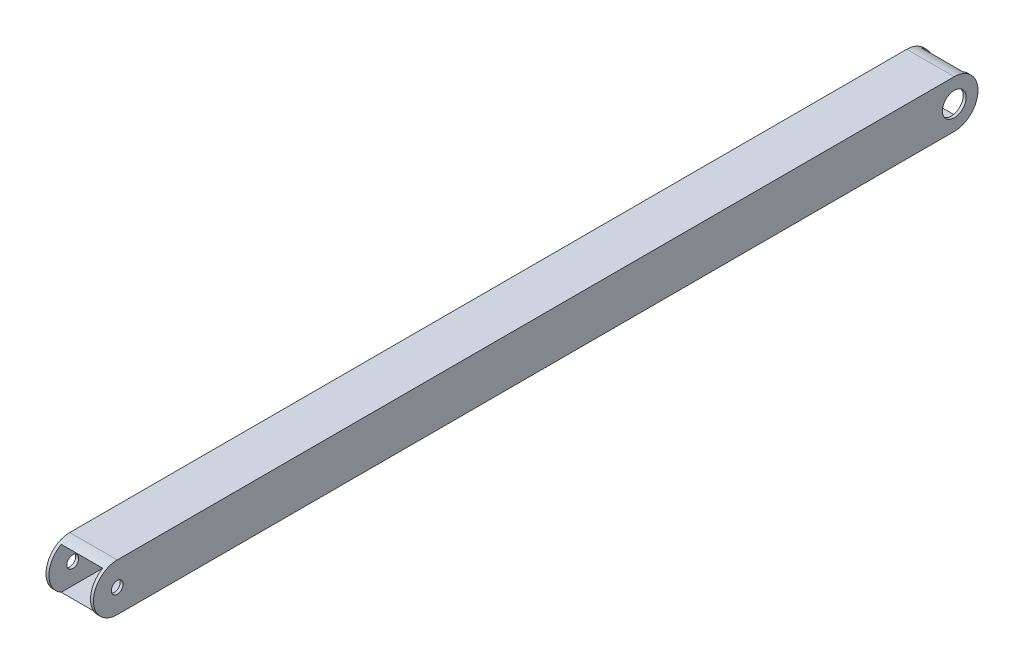
SolidWorks part; units mm, degrees
ref_plane "Front Plane" through (0, 0, 0) normal (0, 0, 1) x (1, 0, 0)
ref_plane "Top Plane" through (0, 0, 0) normal (0, 1, 0) x (1, 0, 0)
ref_plane "Right Plane" through (0, 0, 0) normal (1, 0, 0) x (0, 0, -1)
sketch "Sketch1" plane through (0, 0, 0) normal (0, 0, 1) x (1, 0, 0)
  line L0 (-11.1125, 11.1125) -> (11.1125, 11.1125)
  line L1 (-12.7, 12.7) -> (12.7, 12.7)
  line L2 (-12.7, 12.7) -> (-12.7, -12.7)
  line L3 (-12.7, -12.7) -> (12.7, -12.7)
  line L4 (12.7, 12.7) -> (12.7, -12.7)
  line L5 (-12.7, 12.7) -> (12.7, -12.7) construction
  line L6 (-12.7, -12.7) -> (12.7, 12.7) construction
  line L7 (11.1125, 11.1125) -> (11.1125, -11.1125)
  line L8 (-11.1125, -11.1125) -> (11.1125, -11.1125)
  line L9 (-11.1125, 11.1125) -> (-11.1125, -11.1125)
  point P0 (0, 0)
  dimension "D1" = 25.4
  dimension "D2" = 25.4
  dimension "D3" = 1.5875
extrude "Boss-Extrude1" add sketch "Sketch1" along normal blind 473.2274
sketch "Sketch2" plane through (12.7, 0, 0) normal (1, 0, 0) x (0, 0, -1)
  line L0 (-473.2274, 12.7) -> (-460.5274, 12.7) construction
  line L1 (-473.2274, 12.7) -> (0, 12.7) construction
  line L2 (-460.5274, 12.7) -> (-460.5274, -12.7) construction
  line L3 (-473.2274, -12.7) -> (0, -12.7) construction
  line L4 (-473.2274, 12.7) -> (-460.5274, 12.7)
  line L5 (-473.2274, 12.7) -> (-473.2274, -12.7)
  line L6 (-473.2274, -12.7) -> (-460.5274, -12.7)
  arc A0 (-460.5274, 12.7) -> (-460.5274, -12.7) centre (-460.5274, 0) ccw
  line M3 (0, 12.7) -> (-473.2274, 12.7)
  line M4 (-473.2274, 12.7) -> (-473.2274, -12.7)
  line M5 (-473.2274, -12.7) -> (0, -12.7)
  dimension "D1" = 12.7
extrude "Cut-Extrude1" cut sketch "Sketch2" against normal through all contours A0 M3 M4 | A0 L5 M5
sketch "Sketch3" plane through (12.7, 0, 0) normal (1, 0, 0) x (0, 0, -1)
  line L0 (-460.5274, -12.7) -> (0, -12.7) construction
  circle A0 centre (-460.5274, 0) radius 3.175
  arc A1 (-460.5274, 12.7) -> (-460.5274, -12.7) centre (-460.5274, 0) ccw construction
  circle A2 centre (-12.7, 0) radius 6.35
  dimension "D1" = 6.35
  dimension "D2" = 12.7
  dimension "D4" = 12.7
  dimension "D6" = 12.7
extrude "Cut-Extrude2" cut sketch "Sketch3" against normal through all
sketch "Sketch5" plane through (12.7, 0, 0) normal (1, 0, 0) x (0, 0, -1)
  line L0 (0, 12.7) -> (-12.7, 12.7) construction
  line L1 (-460.5274, 12.7) -> (0, 12.7) construction
  line L2 (-12.7, 12.7) -> (-12.7, -12.7) construction
  line L3 (-460.5274, -12.7) -> (0, -12.7) construction
  line L4 (-12.7, 12.7) -> (0, 12.7)
  line L5 (0, 12.7) -> (0, -12.7)
  line L6 (0, -12.7) -> (-12.7, -12.7)
  arc A0 (-12.7, 12.7) -> (-12.7, -12.7) centre (-12.7, 0) cw
  line M6 (-460.5274, -12.7) -> (0, -12.7)
  line M7 (0, -12.7) -> (0, 12.7)
  line M8 (0, 12.7) -> (-460.5274, 12.7)
  dimension "D1" = 12.7
extrude "Cut-Extrude3" cut sketch "Sketch5" against normal through all contours A0 L5 M8 | A0 M7 M6
